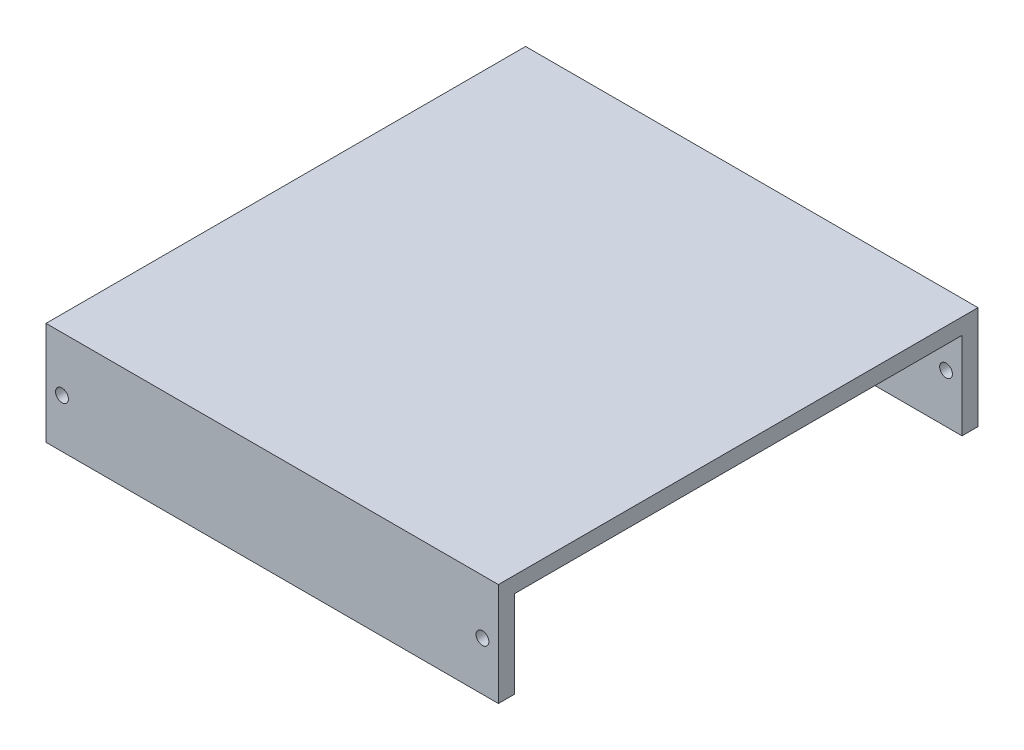
SolidWorks part; units mm, degrees
ref_plane "前视基准面" through (0, 0, 0) normal (0, 0, 1) x (1, 0, 0)
ref_plane "上视基准面" through (0, 0, 0) normal (0, 1, 0) x (1, 0, 0)
ref_plane "右视基准面" through (0, 0, 0) normal (1, 0, 0) x (0, 0, -1)
sketch "草图2" plane through (0, 0, 0) normal (0, 0, 1) x (1, 0, 0)
  line L2 (212.655, 48) -> (-50.345, 48)
  line L4 (212.655, 48) -> (222.655, 48)
  line L5 (222.655, 48) -> (222.655, -3.53)
  line L7 (-50.345, 48) -> (-60.345, 48)
  line L8 (-60.345, 48) -> (-60.345, -3.53)
  line L14 (222.655, -3.53) -> (222.655, -6.47)
  line L15 (222.655, -6.47) -> (-60.345, -6.47)
  line L16 (-60.345, -6.47) -> (-60.345, -3.53)
  circle A0 centre (212.655, 24) radius 4
  circle A1 centre (-50.345, 24) radius 4
extrude "凸台-拉伸1" add sketch "草图2" along normal blind 10
sketch "草图3" plane through (0, 0, 0) normal (0, 0, 1) x (1, 0, 0)
  line L0 (-60.345, 48) -> (-60.345, 58)
  line L1 (-60.345, 58) -> (222.655, 58)
  line L2 (222.655, 58) -> (222.655, 48)
  line L3 (222.655, -6.47) -> (222.655, 48) construction
  line L4 (222.655, 48) -> (-60.345, 48)
extrude "凸台-拉伸5" add sketch "草图3" along normal blind 300
sketch "草图6" plane through (0, 0, 300) normal (0, 0, 1) x (1, 0, 0)
  line L0 (-60.345, 58) -> (-60.345, -6.47)
  line L1 (-60.345, -6.47) -> (222.655, -6.47) construction
  line L2 (-60.345, -6.47) -> (222.655, -6.47)
  line L3 (222.655, -6.47) -> (222.655, 58)
  line L4 (222.655, 58) -> (-60.345, 58)
  circle A0 centre (-50.345, 24) radius 4
  circle A1 centre (212.655, 24) radius 4
extrude "凸台-拉伸7" add sketch "草图6" against normal blind 10
